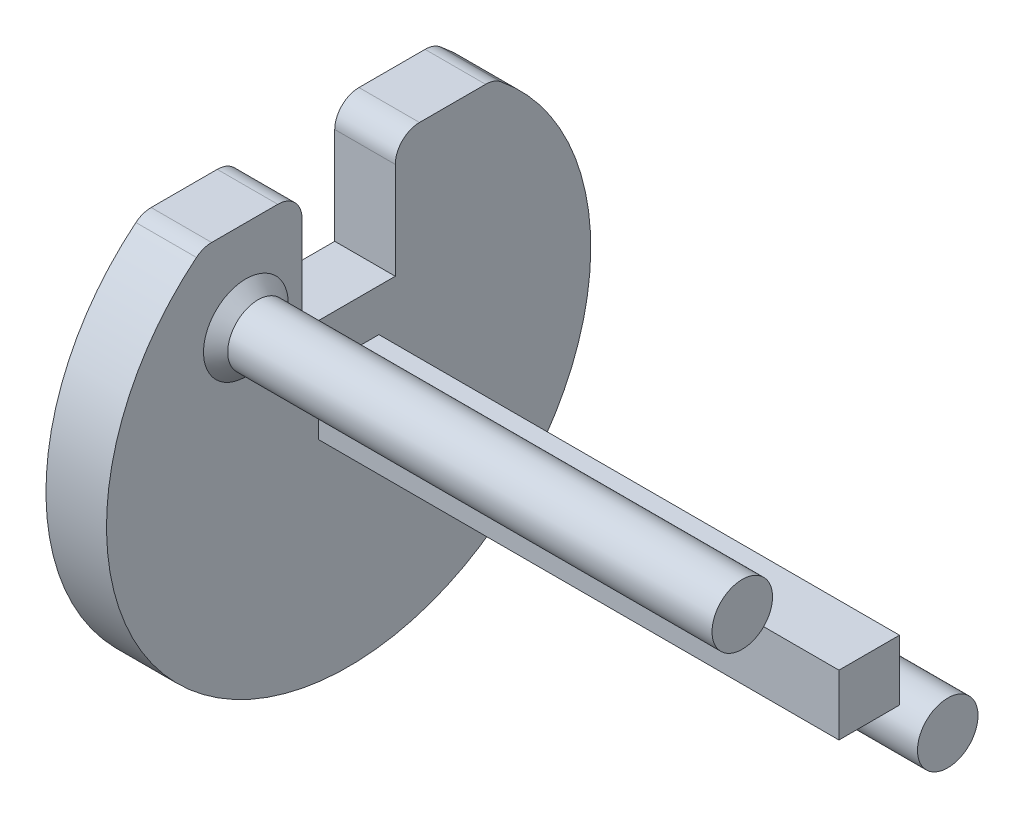
SolidWorks part; units mm, degrees
ref_plane "Front Plane" through (0, 0, 0) normal (0, 0, 1) x (1, 0, 0)
ref_plane "Top Plane" through (0, 0, 0) normal (0, 1, 0) x (1, 0, 0)
ref_plane "Right Plane" through (0, 0, 0) normal (1, 0, 0) x (0, 0, -1)
sketch "Sketch2" plane through (0, 0, 0) normal (1, 0, 0) x (0, 0, -1)
  circle A0 centre (0, 0) radius 20
  dimension "D1" = 40
extrude "Boss-Extrude2" add sketch "Sketch2" along normal blind 5
sketch "Sketch3" plane through (5, 0, 0) normal (1, 0, 0) x (0, 0, -1)
  line L1 (-2.5, -2.5) -> (2.5, -2.5)
  line L2 (-2.5, -2.5) -> (-2.5, 2.5)
  line L3 (-2.5, 2.5) -> (2.5, 2.5)
  line L4 (2.5, -2.5) -> (2.5, 2.5)
  line L5 (-2.5, -2.5) -> (2.5, 2.5) construction
  line L6 (-2.5, 2.5) -> (2.5, -2.5) construction
  point P0 (0, 0)
  dimension "D1" = 5
  dimension "D2" = 5
extrude "Boss-Extrude3" add sketch "Sketch3" along normal blind 43
sketch "Sketch4" plane through (5, 0, 0) normal (1, 0, 0) x (0, 0, -1)
  line L0 (8.4853, -8.4853) -> (-8.4853, 8.4853)
  line L1 (0, 0) -> (0, 50000) construction
  circle A1 centre (-8.4853, 8.4853) radius 2.5
  circle A2 centre (8.4853, -8.4853) radius 2.5
  point P4 (0, 0)
  dimension "D3" = 5
  dimension "D4" = 5
  dimension "D1" = 45
  dimension "D2" = 12
extrude "Boss-Extrude4" add sketch "Sketch4" along normal blind 41
sketch "Sketch5" plane through (5, 0, 0) normal (1, 0, 0) x (0, 0, -1)
  line L0 (2.5, 2.5) -> (-2.5, 2.5) construction
  line L1 (-3.8523, 6) -> (3.8523, 6)
  line L2 (-3.8523, 6) -> (-3.8523, 20)
  line L3 (-3.8523, 20) -> (3.8523, 20)
  line L4 (3.8523, 6) -> (3.8523, 20)
  line L6 (-20, 20) -> (20, 20)
  line L7 (-20, 20) -> (-20, 16)
  line L8 (-20, 16) -> (20, 16)
  line L9 (20, 20) -> (20, 16)
  circle A0 centre (0, 0) radius 20 construction
  point P6 (0, 2.5)
  point P7 (0, 6)
  circle M7 centre (0, 0) radius 20
  dimension "D1" = 14
  dimension "D2" = 4
extrude "Cut-Extrude1" cut sketch "Sketch5" against normal through all contours L8 L2 M7 | L2 L8 L4 M7 | L4 L8 M7 | L8 L2 L1 L4
fillet "Fillet1" radius 2 4 edges at (2.5, 16, -12) (2.5, 16, 12) (2.5, 16, -3.8523) (2.5, 16, 3.8523)
chamfer "Chamfer1" distance 1 angle 45 2 edges at (5, -8.4853, -10.9853) (5, 8.4853, 5.9853)
